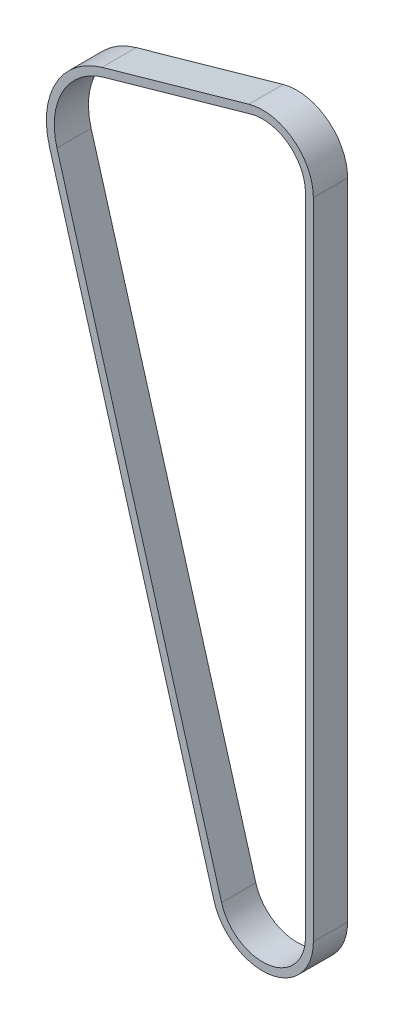
SolidWorks part; units mm, degrees
ref_plane "Front Plane" through (0, 0, 0) normal (0, 0, 1) x (1, 0, 0)
ref_plane "Top Plane" through (0, 0, 0) normal (0, 1, 0) x (1, 0, 0)
ref_plane "Right Plane" through (0, 0, 0) normal (1, 0, 0) x (0, 0, -1)
sketch "Sketch1" plane through (0, 0, 0) normal (0, 0, 1) x (1, 0, 0)
  line L0 (-13.2839, 56.4124) -> (12.4767, 63.6985)
  line L1 (22.0176, -51.5753) -> (22.0179, -51.6486)
  line L2 (-21.5483, 41.5411) -> (7.3115, -58.5593)
  line L3 (22.0179, 56.4816) -> (22.0179, -56.4816)
  arc A0 (22.0179, -51.6486) -> (22.0176, -51.5753) centre (14.5179, -51.6486) ccw
  arc A1 (22.0179, 56.4816) -> (12.4767, 63.6985) centre (14.5179, 56.4816) ccw
  arc A2 (7.3115, -58.5593) -> (22.0179, -56.4816) centre (14.5179, -56.4816) ccw
  arc A3 (-13.2839, 56.4124) -> (-21.5483, 41.5411) centre (-10.0179, 44.8654) ccw
extrude "Extrude-Thin1" add sketch "Sketch1" along normal blind 6 thin contours L0 A1 L3 A2 L2 A3
